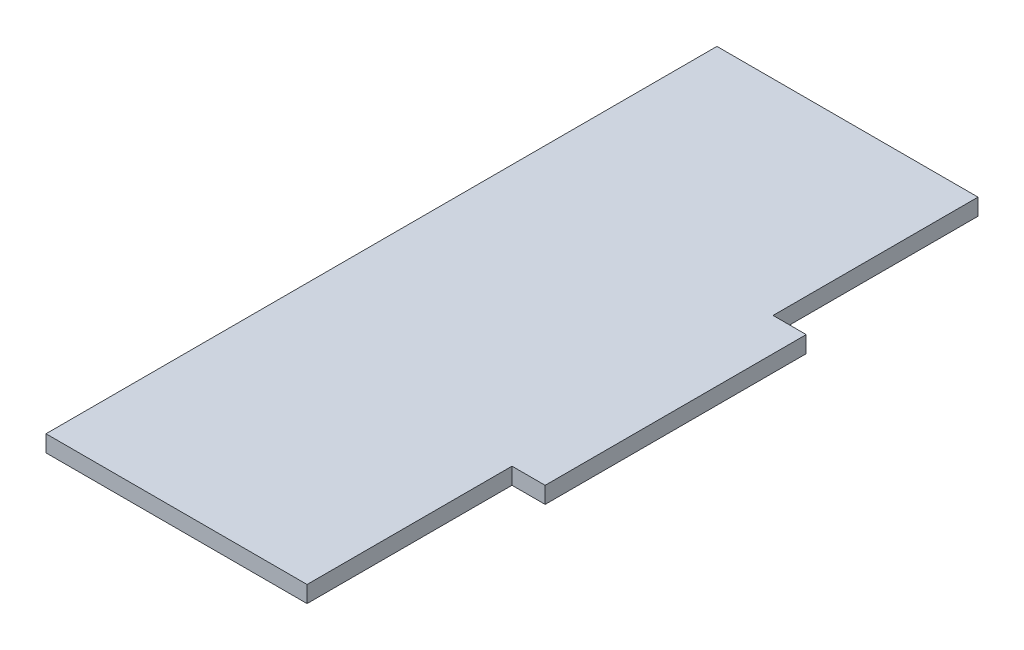
SolidWorks part; units mm, degrees
material "Cedar"
ref_plane "Front Plane" through (0, 0, 0) normal (0, 0, 1) x (1, 0, 0)
ref_plane "Top Plane" through (0, 0, 0) normal (0, 1, 0) x (1, 0, 0)
ref_plane "Right Plane" through (0, 0, 0) normal (1, 0, 0) x (0, 0, -1)
sketch "Sketch1" plane through (0, 0, 0) normal (0, 1, 0) x (1, 0, 0)
  line L0 (-25, 39.25) -> (25, 39.25)
  line L1 (25, 39.25) -> (25, 0)
  line L2 (25, 0) -> (31.35, 0)
  line L3 (31.35, 0) -> (31.35, -50)
  line L4 (31.35, -50) -> (25, -50)
  line L5 (25, -50) -> (25, -89.25)
  line L6 (25, -89.25) -> (-25, -89.25)
  line L7 (-25, -89.25) -> (-25, -50)
  line L8 (-25, -50) -> (-31.35, -50)
  line L9 (-31.35, -50) -> (-31.35, 0)
  line L10 (-31.35, 0) -> (-25, 0)
  line L11 (-25, 0) -> (-25, 39.25)
  line L12 (-25, 0) -> (-25, -50) construction
  point P11 (0, 39.25)
  point P14 (-31.35, -25)
  dimension "D1" = 6.35
  dimension "D2" = 50
  dimension "D3" = 50
  dimension "D4" = 128.5
extrude "Boss-Extrude1" add sketch "Sketch1" along normal blind 3.175 contours L11 L12 L7 L6 L5 L4 L3 L2 L1 L0
equation "\"length\"= 128.5mm"
equation "\"w_mach\"= 50mm"
equation "\"w_tab\"= 50mm"
equation "\"t_wood\"= 0.125in"
equation "\"t_side\"= 0.25in"
equation "\"D1@Sketch1\"=\"t_side\""
equation "\"D2@Sketch1\"=\"w_tab\""
equation "\"D3@Sketch1\"=\"w_mach\""
equation "\"D4@Sketch1\"=\"length\""
equation "\"D1@Boss-Extrude1\"=\"t_wood\""
